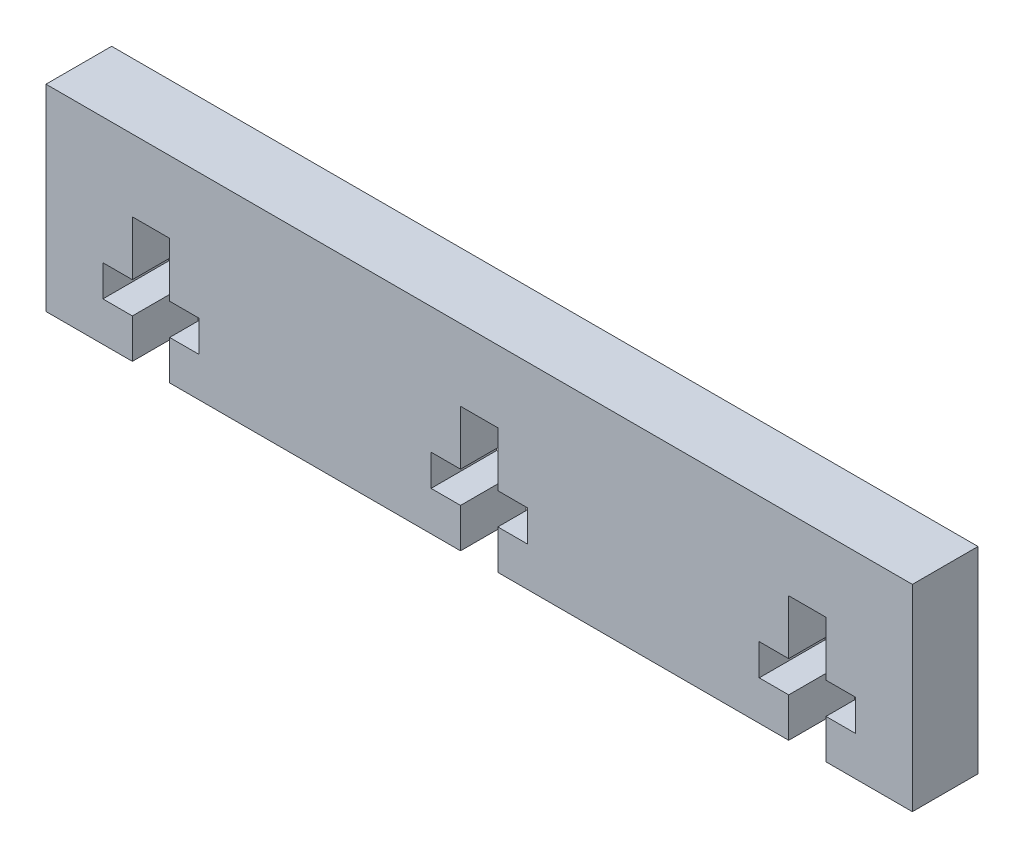
SolidWorks part; units mm, degrees
ref_plane "Front Plane" through (0, 0, 0) normal (0, 0, 1) x (1, 0, 0)
ref_plane "Top Plane" through (0, 0, 0) normal (0, 1, 0) x (1, 0, 0)
ref_plane "Right Plane" through (0, 0, 0) normal (1, 0, 0) x (0, 0, -1)
sketch "Sketch1" plane through (0, 0, 0) normal (0, 0, 1) x (1, 0, 0)
  line L0 (33, -13.137) -> (33, 28.9045) construction
  line L1 (0, 0) -> (6.58, 0)
  line L2 (0, 0) -> (0, 15)
  line L3 (0, 15) -> (66, 15)
  line L4 (66, 0) -> (66, 15)
  line L5 (8, 23.8211) -> (8, -4.3534) construction
  line L6 (58, 19.8273) -> (58, -5.0563) construction
  line L7 (6.58, 0) -> (6.58, 3)
  line L8 (6.58, 3) -> (4.335, 3)
  line L9 (4.335, 3) -> (4.335, 5.39)
  line L10 (4.335, 5.39) -> (6.58, 5.39)
  line L11 (6.58, 5.39) -> (6.58, 9.54)
  line L12 (6.58, 9.54) -> (9.42, 9.54)
  line L13 (9.42, 0) -> (9.42, 3)
  line L14 (9.42, 3) -> (11.665, 3)
  line L15 (11.665, 3) -> (11.665, 5.39)
  line L16 (11.665, 5.39) -> (9.42, 5.39)
  line L17 (9.42, 5.39) -> (9.42, 9.54)
  line L18 (54.335, 5.39) -> (56.58, 5.39)
  line L19 (54.335, 3) -> (54.335, 5.39)
  line L20 (56.58, 3) -> (54.335, 3)
  line L21 (56.58, 0) -> (56.58, 3)
  line L22 (59.42, 0) -> (59.42, 3)
  line L23 (59.42, 3) -> (61.665, 3)
  line L24 (61.665, 3) -> (61.665, 5.39)
  line L25 (61.665, 5.39) -> (59.42, 5.39)
  line L26 (59.42, 5.39) -> (59.42, 9.54)
  line L27 (59.42, 9.54) -> (56.58, 9.54)
  line L28 (56.58, 5.39) -> (56.58, 9.54)
  line L29 (34.42, 5.39) -> (34.42, 9.54)
  line L30 (34.42, 9.54) -> (31.58, 9.54)
  line L31 (31.58, 5.39) -> (31.58, 9.54)
  line L32 (29.335, 5.39) -> (31.58, 5.39)
  line L33 (29.335, 3) -> (29.335, 5.39)
  line L34 (31.58, 3) -> (29.335, 3)
  line L35 (31.58, 0) -> (31.58, 3)
  line L36 (34.42, 0) -> (34.42, 3)
  line L37 (34.42, 3) -> (36.665, 3)
  line L38 (36.665, 3) -> (36.665, 5.39)
  line L39 (9.42, 0) -> (31.58, 0)
  line L40 (34.42, 0) -> (56.58, 0)
  line L41 (59.42, 0) -> (66, 0)
  line L42 (34.42, 5.39) -> (36.665, 5.39)
  point P24 (8, 9.54)
  dimension "D1" = 1.42
  dimension "D2" = 25
  dimension "D3" = 25
  dimension "D4" = 8
  dimension "D5" = 8
  dimension "D6" = 3
  dimension "D7" = 2.39
  dimension "D8" = 4.15
  dimension "D9" = 3.665
  dimension "D10" = 2
extrude "Boss-Extrude1" add sketch "Sketch1" along normal blind 5
